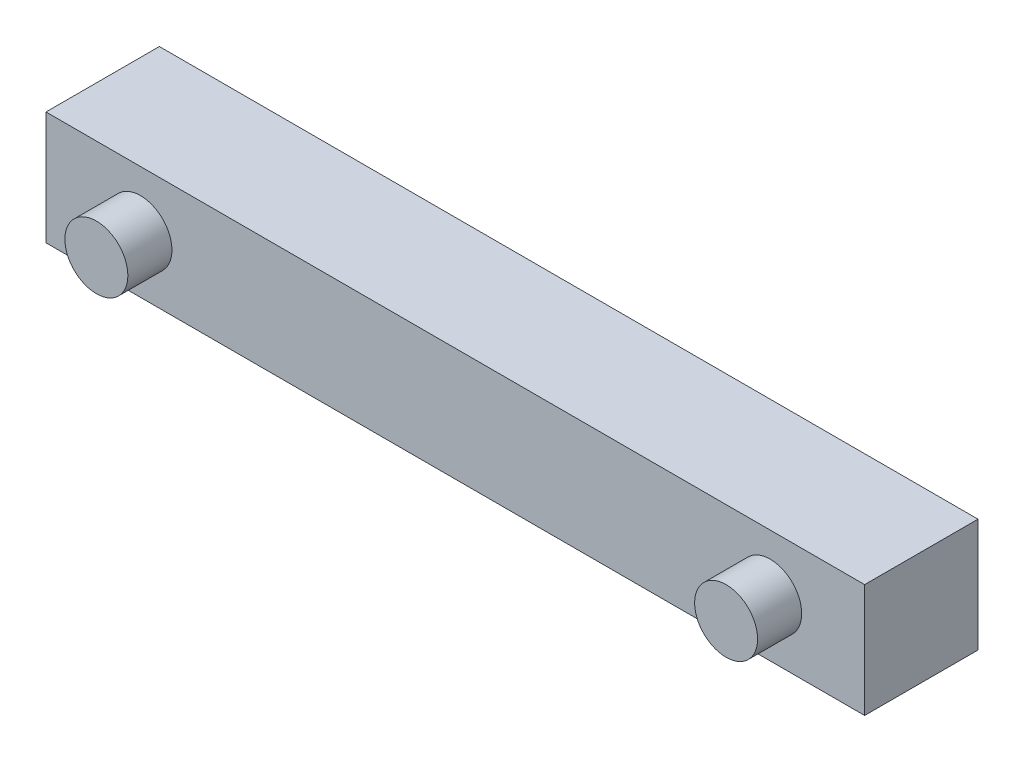
SolidWorks part; units mm, degrees
ref_plane "Front Plane" through (0, 0, 0) normal (0, 0, 1) x (1, 0, 0)
ref_plane "Top Plane" through (0, 0, 0) normal (0, 1, 0) x (1, 0, 0)
ref_plane "Right Plane" through (0, 0, 0) normal (1, 0, 0) x (0, 0, -1)
sketch "Sketch1" plane through (0, 0, 0) normal (0, 0, 1) x (1, 0, 0)
  line L1 (0, 0) -> (65, 0)
  line L2 (0, 0) -> (0, 9)
  line L3 (0, 9) -> (65, 9)
  line L4 (65, 0) -> (65, 9)
  dimension "D1" = 65
  dimension "D2" = 9
extrude "Boss-Extrude1" add sketch "Sketch1" along normal blind 9
sketch "Sketch2" plane through (0, 0, 9) normal (0, 0, 1) x (1, 0, 0)
  line L0 (0, 0) -> (65, 0) construction
  line L1 (0, 9) -> (0, 0) construction
  circle A0 centre (7.5, 4.5) radius 2.5
  circle A1 centre (57.5, 4.5) radius 2.5
  dimension "D1" = 5
  dimension "D2" = 5
  dimension "D3" = 50
  dimension "D5" = 4.5
  dimension "D6" = 7.5
extrude "Boss-Extrude2" add sketch "Sketch2" along normal blind 3.5
